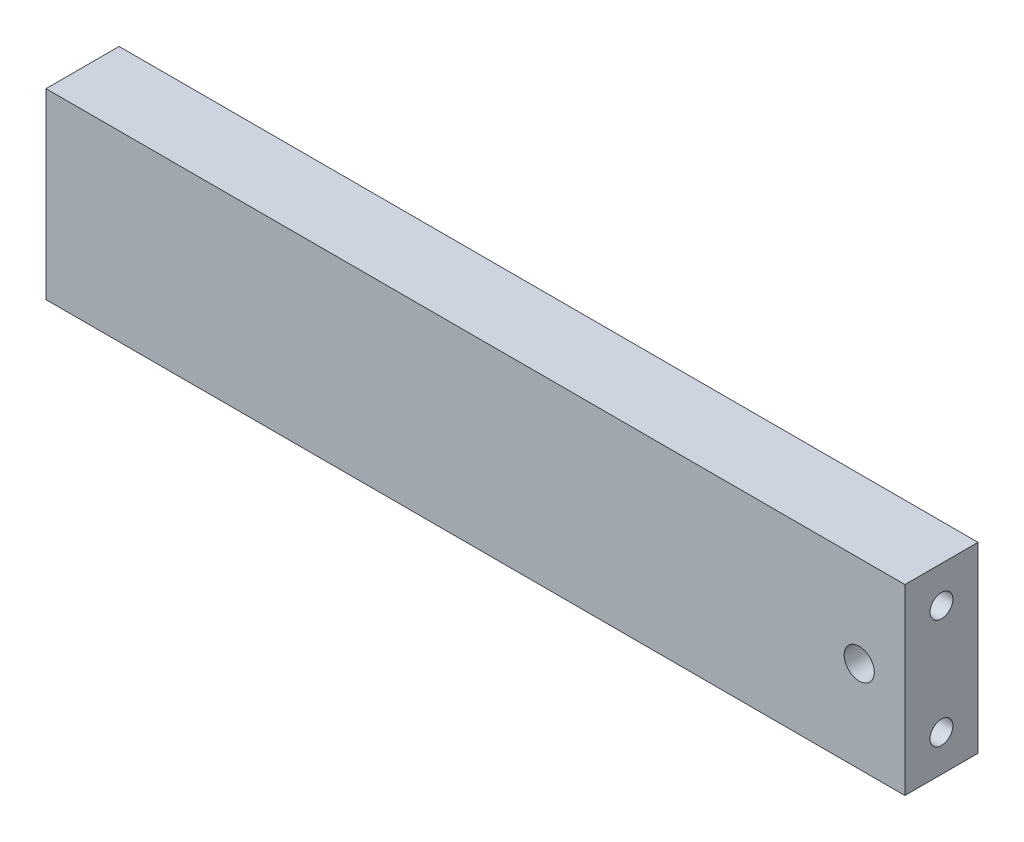
SolidWorks part; units mm, degrees
ref_plane "정면" through (0, 0, 0) normal (0, 0, 1) x (1, 0, 0)
ref_plane "윗면" through (0, 0, 0) normal (0, 1, 0) x (1, 0, 0)
ref_plane "우측면" through (0, 0, 0) normal (1, 0, 0) x (0, 0, -1)
sketch "스케치1" plane through (0, 0, 0) normal (0, 0, 1) x (1, 0, 0)
  line L1 (-47, 10) -> (47, 10)
  line L2 (-47, 10) -> (-47, -10)
  line L3 (-47, -10) -> (47, -10)
  line L4 (47, 10) -> (47, -10)
  line L5 (-47, 10) -> (47, -10) construction
  line L6 (-47, -10) -> (47, 10) construction
  point P0 (0, 0)
  dimension "D1" = 94
  dimension "D2" = 20
extrude "보스-돌출1" add sketch "스케치1" along normal blind 8
hole_wizard "M4-ALTADJUST" positions "스케치2" profile "스케치3" tap size "M4" standard "ISO" end condition up to next
sketch "스케치2" plane through (0, 0, 8) normal (0, 0, 1) x (1, 0, 0)
  line L6 (47, -10) -> (47, 10) construction
  point P7 (42, 0)
  point P26 (47, 0)
  dimension "D1" = 5
sketch "스케치3" plane through (42, 0, 8) normal (1, 0, 0) x (0, -1, 0)
  line L0 (0, 0) -> (0, 8)
  line L1 (0, 8) -> (1.65, 8)
  line L2 (1.65, 8) -> (1.65, 0)
  line L5 (1.65, 0) -> (0, 0)
  line L11 (0, -6.35) -> (0, 107.95) construction
  dimension "관통 탭 드릴 지름" = 3.3
  dimension "관통 탭 드릴 깊이" = 8
cosmetic thread "구멍 나사산1" parameters "D2"=4
hole_wizard "M3-HORIZONTALBAR_FIX" positions "스케치4" profile "스케치5" tap size "M3" standard "ISO"
sketch "스케치4" plane through (47, 0, 0) normal (1, 0, 0) x (0, 0, -1)
  line L0 (-4, 6) -> (-4, -6)
  line L2 (0, -10) -> (0, 10) construction
  line L3 (-8, 10) -> (0, 10) construction
  point P0 (-4, 6)
  point P2 (-4, -6)
  point P9 (-4, 0)
  point P12 (0, 0)
  point P15 (-4, 10)
  dimension "D1" = 4
sketch "스케치5" plane through (47, 6, 4) normal (0, 1, 0) x (0, 0, -1)
  line L0 (0, 0) -> (0, 9.2511)
  line L1 (0, 9.2511) -> (1.25, 8.5)
  line L2 (1.25, 8.5) -> (1.25, 0)
  line L5 (1.25, 0) -> (0, 0)
  line L10 (0, 9.2511) -> (-1.25, 8.5) construction
  line L11 (0, -6.35) -> (0, 107.95) construction
  dimension "탭 드릴 지름" = 2.5
  dimension "탭 드릴 깊이" = 8.5
  dimension "드릴 각도" = 118
cosmetic thread "구멍 나사산2" parameters "D1"=6, "D2"=3
cosmetic thread "구멍 나사산3" parameters "D1"=6, "D2"=3
ref_plane "평면1" through (0, 0, 0) normal (1, 0, 0) x (0, 0, -1)
mirror "대칭 복사1" about plane through (0, 0, 0) normal (1, 0, 0) of "M3-HORIZONTALBAR_FIX"
cosmetic thread "구멍 나사산4" parameters "D1"=6, "D2"=3
cosmetic thread "구멍 나사산5" parameters "D1"=6, "D2"=3
